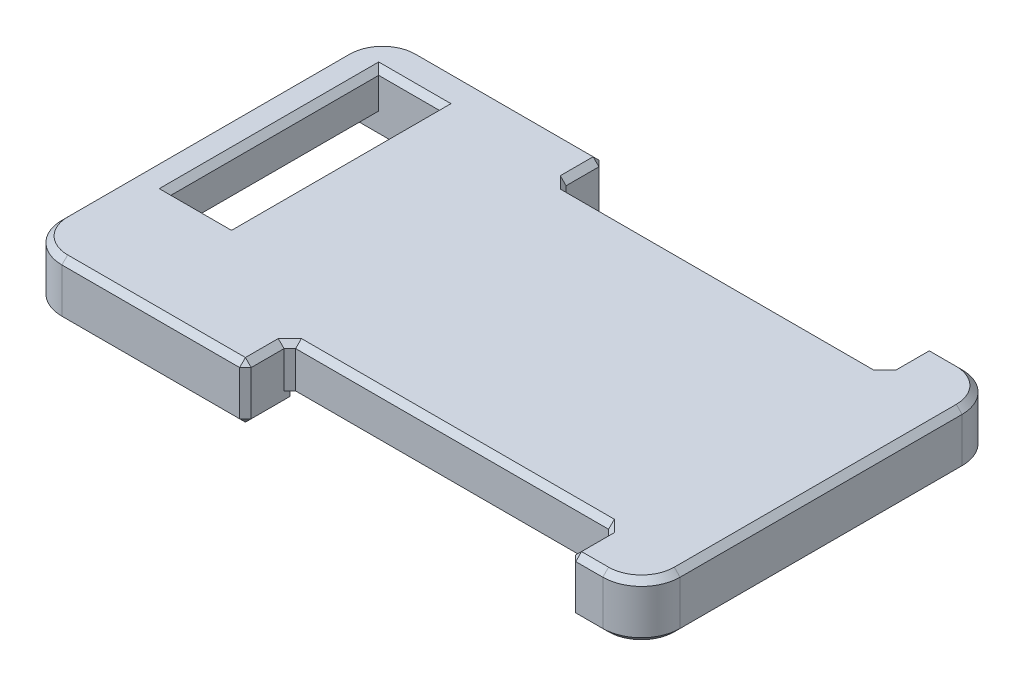
SolidWorks part; units mm, degrees
ref_plane "前视基准面" through (0, 0, 0) normal (0, 0, 1) x (1, 0, 0)
ref_plane "上视基准面" through (0, 0, 0) normal (0, 1, 0) x (1, 0, 0)
ref_plane "右视基准面" through (0, 0, 0) normal (1, 0, 0) x (0, 0, -1)
sketch "草图1" plane through (0, 0, 0) normal (0, 1, 0) x (1, 0, 0)
  line L0 (31.2799, 0) -> (63.2799, 0)
  line L1 (63.2799, 0) -> (63.2799, 18.6)
  line L2 (63.2799, 18.6) -> (31.2799, 18.6)
  line L3 (31.2799, 18.6) -> (31.2799, 0)
extrude "凸台-拉伸1" add sketch "草图1" along normal blind 2.2
fillet "圆角1" radius 2 4 edges at (31.2799, 1.1, 0) (31.2799, 1.1, -18.6) (63.2799, 1.1, -18.6) (63.2799, 1.1, 0)
sketch "草图2" plane through (0, 2.2, 0) normal (0, 1, 0) x (1, 0, 0)
  line L18 (36.1199, 16.7) -> (32.9799, 16.7)
  line L19 (32.9799, 16.7) -> (32.9799, 5.94)
  line L20 (32.9799, 5.94) -> (36.1199, 5.94)
  line L21 (36.1199, 5.94) -> (36.1199, 16.7)
  line L22 (42.7799, -0.3) -> (42.7799, 2.3)
  line L23 (42.7799, 2.3) -> (59.5799, 2.3)
  line L24 (59.5799, 2.3) -> (59.5799, -0.3)
  line L25 (42.7799, -0.3) -> (59.5799, -0.3)
  line L26 (59.5799, 18.9) -> (59.5799, 16.3)
  line L27 (59.5799, 16.3) -> (42.7799, 16.3)
  line L28 (42.7799, 16.3) -> (42.7799, 18.9)
  line L29 (42.7799, 18.9) -> (59.5799, 18.9)
extrude "切除-拉伸1" cut sketch "草图2" against normal through all
sketch "草图3" plane through (0, 0, 0) normal (0, -1, 0) x (1, 0, 0)
  line L0 (32.9799, -5.94) -> (36.1199, -5.94) construction
  line L1 (32.9799, -16.7) -> (32.9799, -5.94) construction
  line L2 (36.1199, -16.7) -> (32.9799, -16.7) construction
  line L3 (36.1199, -5.94) -> (36.1199, -2.3)
  line L4 (32.9799, -5.94) -> (36.1199, -5.94)
  line L5 (32.9799, -16.7) -> (32.9799, -5.94)
  line L6 (36.1199, -16.7) -> (32.9799, -16.7)
  line L11 (42.7799, -16.3) -> (36.1199, -16.3)
  line L12 (59.5799, -2.3) -> (42.7799, -2.3)
  line L13 (42.7799, -2.3) -> (42.7799, 0)
  line L14 (42.7799, 0) -> (33.2799, 0)
  line L15 (31.2799, -2) -> (31.2799, -16.6)
  line L16 (33.2799, -18.6) -> (42.7799, -18.6)
  line L17 (42.7799, -18.6) -> (42.7799, -16.3)
  line L18 (42.7799, -16.3) -> (59.5799, -16.3)
  line L19 (59.5799, -16.3) -> (59.5799, -18.6)
  line L20 (59.5799, -18.6) -> (61.2799, -18.6)
  line L21 (63.2799, -16.6) -> (63.2799, -2)
  line L22 (61.2799, 0) -> (59.5799, 0)
  line L23 (59.5799, 0) -> (59.5799, -2.3)
  line L25 (42.7799, -2.3) -> (42.7799, 0)
  line L26 (42.7799, 0) -> (33.2799, 0)
  line L28 (33.2799, -18.6) -> (42.7799, -18.6)
  line L29 (42.7799, -18.6) -> (42.7799, -16.3)
  line L31 (59.5799, -16.3) -> (59.5799, -18.6)
  line L32 (59.5799, -18.6) -> (61.2799, -18.6)
  line L33 (63.2799, -16.6) -> (63.2799, -2)
  line L34 (61.2799, 0) -> (59.5799, 0)
  line L35 (59.5799, 0) -> (59.5799, -2.3)
  line L38 (59.5799, -2.3) -> (59.5799, -16.3)
  line L40 (36.1199, -5.94) -> (36.1199, -16.7) construction
  line L42 (36.1199, -16.3) -> (36.1199, -16.7)
  line L43 (31.2799, -16.6) -> (31.2799, -2)
  line L44 (36.1199, -2.3) -> (42.7799, -2.3)
  arc A4 (33.2799, 0) -> (31.2799, -2) centre (33.2799, -2) ccw
  arc A5 (31.2799, -16.6) -> (33.2799, -18.6) centre (33.2799, -16.6) ccw
  arc A6 (61.2799, -18.6) -> (63.2799, -16.6) centre (61.2799, -16.6) ccw
  arc A7 (63.2799, -2) -> (61.2799, 0) centre (61.2799, -2) ccw
  arc A8 (33.2799, 0) -> (31.2799, -2) centre (33.2799, -2) ccw
  arc A9 (31.2799, -16.6) -> (33.2799, -18.6) centre (33.2799, -16.6) ccw
  arc A10 (61.2799, -18.6) -> (63.2799, -16.6) centre (61.2799, -16.6) ccw
  arc A11 (63.2799, -2) -> (61.2799, 0) centre (61.2799, -2) ccw
  dimension "D1" = 0
extrude "凸台-拉伸2" add sketch "草图3" along normal blind 0.7
chamfer "倒角1" distance 0.3 angle 45 45 edges at (36.1199, -0.7, -4.12) (34.5499, -0.7, -5.94) (39.4499, -0.7, -16.3) (42.7799, -0.7, -17.45) (38.0299, -0.7, -18.6) (31.8657, -0.7, -18.0142) (31.2799, -0.7, -9.3) (31.8657, -0.7, -0.5858) (38.0299, -0.7, 0) (42.7799, -0.7, -1.15) (39.4499, -0.7, -2.3) (60.4299, -0.7, 0) (62.6941, -0.7, -0.5858) (63.2799, -0.7, -9.3) (62.6941, -0.7, -18.0142) (60.4299, -0.7, -18.6) (59.5799, -0.7, -9.3) (38.0299, 2.2, 0) (31.8657, 2.2, -0.5858) (31.2799, 2.2, -9.3) (31.8657, 2.2, -18.0142) (38.0299, 2.2, -18.6) (42.7799, 2.2, -17.45) (51.1799, 2.2, -16.3) (59.5799, 2.2, -17.45) (60.4299, 2.2, -18.6) (62.6941, 2.2, -18.0142) (63.2799, 2.2, -9.3) (62.6941, 2.2, -0.5858) (60.4299, 2.2, 0) (59.5799, 2.2, -1.15) (51.1799, 2.2, -2.3) (42.7799, 2.2, -1.15) (34.5499, 2.2, -16.7) (32.9799, 2.2, -11.32) (34.5499, 2.2, -5.94) (36.1199, 2.2, -11.32) (42.7799, 0.75, -18.6) (42.7799, 1.1, -16.3) (59.5799, 1.1, -16.3) (59.5799, 0.75, -18.6) (59.5799, 0.75, 0) (59.5799, 1.1, -2.3) (42.7799, 1.1, -2.3) (42.7799, 0.75, 0)
chamfer "倒角2" distance 1 angle 45 1 edges at (32.9799, -0.7, -11.17)
